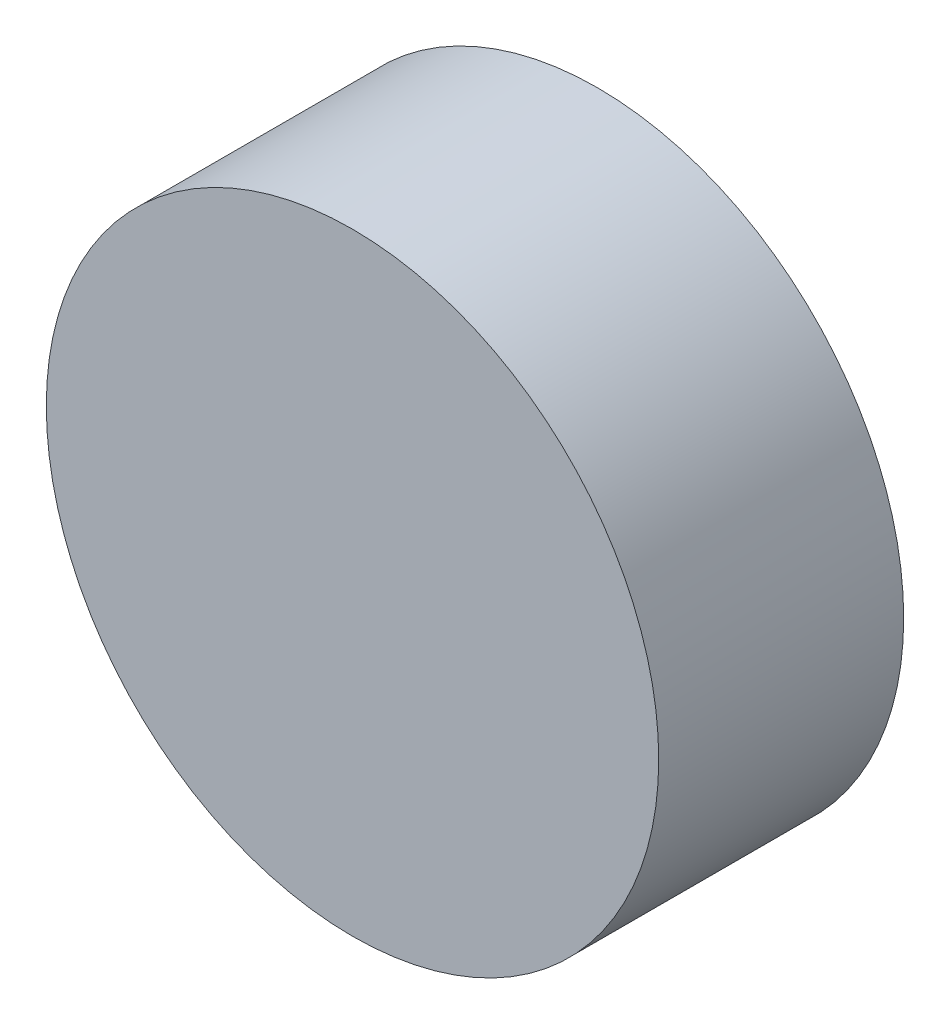
SolidWorks part; units mm, degrees
ref_plane "前视基准面" through (0, 0, 0) normal (0, 0, 1) x (1, 0, 0)
ref_plane "上视基准面" through (0, 0, 0) normal (0, 1, 0) x (1, 0, 0)
ref_plane "右视基准面" through (0, 0, 0) normal (1, 0, 0) x (0, 0, -1)
sketch "草图1" plane through (0, 0, 0) normal (0, 0, 1) x (1, 0, 0)
  circle A0 centre (0, 0) radius 2.5
extrude "凸台-拉伸1" add sketch "草图1" along normal blind 2
